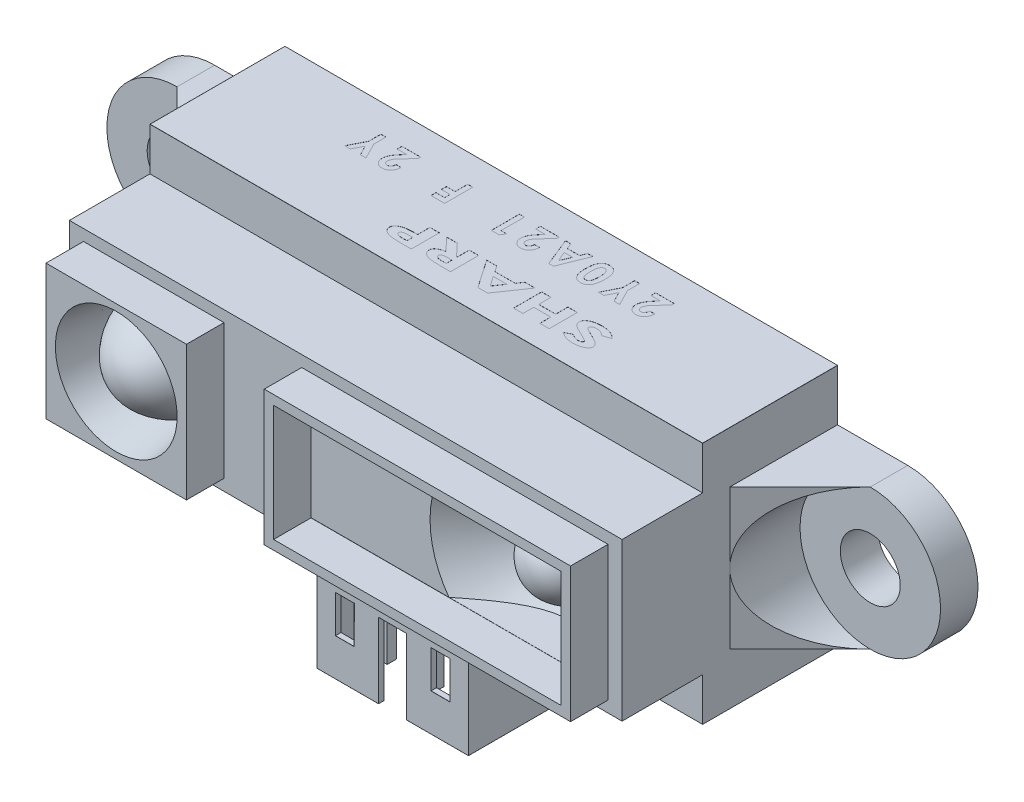
SolidWorks part; units mm, degrees
ref_plane "Front Plane" through (0, 0, 0) normal (0, 0, 1) x (1, 0, 0)
ref_plane "Top Plane" through (0, 0, 0) normal (0, 1, 0) x (1, 0, 0)
ref_plane "Right Plane" through (0, 0, 0) normal (1, 0, 0) x (0, 0, -1)
sketch "Sketch1" plane through (0, 0, 0) normal (0, 0, 1) x (1, 0, 0)
  line L0 (-18.5, 3.75) -> (-14.75, 3.75)
  line L1 (-14.75, -6.5) -> (14.75, -6.5)
  line L2 (-14.75, -6.5) -> (-14.75, -3.75)
  line L3 (-14.75, 6.5) -> (14.75, 6.5)
  line L4 (14.75, -6.5) -> (14.75, -3.75)
  line L5 (0, 0) -> (14.75, 6.5) construction
  line L6 (-14.75, 6.5) -> (0, 0) construction
  line L7 (-18.5, -3.75) -> (-14.75, -3.75)
  line L8 (18.5, -3.75) -> (14.75, -3.75)
  line L9 (18.5, 3.75) -> (14.75, 3.75)
  line L10 (-14.75, 3.75) -> (-14.75, 6.5)
  line L11 (14.75, 3.75) -> (14.75, 6.5)
  line L12 (0, 25.5423) -> (0, -14.0261) construction
  arc A0 (-18.5, 3.75) -> (-18.5, -3.75) centre (-18.5, 0) ccw
  arc A1 (18.5, -3.75) -> (18.5, 3.75) centre (18.5, 0) ccw
  circle A2 centre (-18.5, 0) radius 1.6
  circle A3 centre (18.5, 0) radius 1.6
  point P4 (0, 0)
  dimension "D2" = 37
  dimension "D3" = 18.5
  dimension "D4" = 7.5
  dimension "D5" = 7.5
  dimension "D7" = 3.2
  dimension "D8" = 3.2
  dimension "D1" = 29.5
  dimension "D6" = 13
extrude "Boss-Extrude1" add sketch "Sketch1" along normal blind 13.5
sketch "Sketch3" plane through (0, 0, 0) normal (0, 0, -1) x (-1, 0, 0)
  circle A0 centre (-18.5, 0) radius 3.75
  circle A1 centre (18.5, 0) radius 3.75
extrude "Cut-Extrude1" cut sketch "Sketch3" against normal through all from offset 2 offset against normal yes
sketch "Sketch4" plane through (0, -3.75, 0) normal (0, -1, 0) x (1, 0, 0)
  line L0 (22.25, 2) -> (18.5, 2)
  line L1 (18.5, 2) -> (14.75, 5.75)
  line L2 (14.75, 13.5) -> (14.75, 0) construction
  line L3 (14.75, 5.75) -> (14.75, 13.5)
  line L4 (14.75, 13.5) -> (22.25, 13.5)
  line L5 (22.25, 13.5) -> (22.25, 2)
  line L6 (-22.25, 2) -> (-18.5, 2)
  line L7 (-18.5, 2) -> (-14.75, 5.75)
  line L8 (-14.75, 13.5) -> (-14.75, 0) construction
  line L9 (-14.75, 5.75) -> (-14.75, 13.5)
  line L10 (-14.75, 13.5) -> (-22.25, 13.5)
  line L11 (-22.25, 13.5) -> (-22.25, 2)
  line L12 (14.75, 13.5) -> (14.75, 0) construction
  dimension "D1" = 45
  dimension "D2" = 45
extrude "Cut-Extrude2" cut sketch "Sketch4" against normal through all
sketch "Sketch5" plane through (0, 0, 13.5) normal (0, 0, 1) x (1, 0, 0)
  line L0 (14.75, -6.5) -> (14.75, 6.5) construction
  line L1 (-14.75, 6.5) -> (14.75, 6.5)
  line L2 (-14.75, 6.5) -> (-14.75, 4.2)
  line L3 (-14.75, 4.2) -> (14.75, 4.2)
  line L4 (14.75, 6.5) -> (14.75, 4.2)
  line L6 (-14.75, -6.5) -> (14.75, -6.5)
  line L7 (-14.75, -6.5) -> (-14.75, -4.2)
  line L8 (-14.75, -4.2) -> (14.75, -4.2)
  line L9 (14.75, -6.5) -> (14.75, -4.2)
  dimension "D1" = 8.4
  dimension "D2" = 4.2
extrude "Cut-Extrude3" cut sketch "Sketch5" along normal through all from offset 6.3 offset against normal yes
sketch "Sketch6" plane through (0, 0, 13.5) normal (0, 0, 1) x (1, 0, 0)
  line L0 (-14.75, 4.2) -> (-14.75, -4.2) construction
  line L1 (-14, -3.6) -> (-6.5, -3.6)
  line L2 (-14, -3.6) -> (-14, 3.6)
  line L3 (-14, 3.6) -> (-6.5, 3.6)
  line L4 (14, -3.6) -> (14, 3.6)
  line L5 (-14, -3.6) -> (14, 3.6) construction
  line L6 (-14, 3.6) -> (14, -3.6) construction
  line L7 (-6.5, 3.6) -> (-6.5, -3.6)
  line L8 (-2.35, 3.6) -> (-2.35, -3.6)
  line L9 (-2.35, 3.6) -> (14, 3.6)
  line L10 (-2.35, -3.6) -> (14, -3.6)
  line L12 (-14.75, -4.2) -> (14.75, -4.2)
  line L13 (-14.75, -4.2) -> (-14.75, 4.2)
  line L14 (-14.75, 4.2) -> (14.75, 4.2)
  line L15 (14.75, -4.2) -> (14.75, 4.2)
  line L16 (-14.75, -4.2) -> (14.75, 4.2) construction
  line L17 (-14.75, 4.2) -> (14.75, -4.2) construction
  point P0 (0, 0)
  point P12 (0, 0)
  dimension "D1" = 7.2
  dimension "D2" = 0.75
  dimension "D3" = 7.5
  dimension "D4" = 4.15
  dimension "D5" = 16.35
extrude "Cut-Extrude4" cut sketch "Sketch6" along normal through all from offset 2 offset against normal yes
sketch "Sketch7" plane through (0, 0, 13.5) normal (0, 0, 1) x (1, 0, 0)
  line L0 (-6.5, -3.6) -> (-6.5, 3.6) construction
  line L1 (-6.5, 3.6) -> (-14, 3.6) construction
  circle A0 centre (-10.25, 0) radius 3.25
  point P4 (-6.5, 0)
  point P8 (-10.25, 3.6)
  dimension "D1" = 6.5
extrude "Cut-Extrude5" cut sketch "Sketch7" against normal blind 3 draft 10
sketch "Sketch8" plane through (0, 0, 0) normal (0, 1, 0) x (1, 0, 0)
  line L0 (-10.25, -10.5) -> (-10.25, -17.4091) construction
  line L1 (-12.971, -10.5) -> (-7.529, -10.5) construction
  line L2 (-10.25, -10.5) -> (-7.529, -10.5)
  line L3 (-14, -13.5) -> (-6.5, -13.5) construction
  line L4 (-13.25, -13.5) -> (-7.25, -13.5) construction
  line L5 (-7.529, -13.5) -> (-7.529, -7.5) construction
  line L6 (-10.25, -10.5) -> (-10.25, -13.5)
  spline S0 degree 3 poles (-7.529, -10.5) (-7.529, -11.5) (-8.5833, -13.5) (-10.25, -13.5) knots 0 0 0 0 1 1 1 1
  dimension "D1" = 5
  dimension "D2" = 3
  dimension "D3" = 90
  dimension "D4" = 90
revolve "Revolve1" add sketch "Sketch8" angle 360 about L0
sketch "Sketch9" plane through (0, 0, 13.5) normal (0, 0, 1) x (1, 0, 0)
  line L0 (14, 3.6) -> (-2.35, 3.6) construction
  line L1 (-1.85, -3.1) -> (13.5, -3.1)
  line L2 (-1.85, -3.1) -> (-1.85, 3.1)
  line L3 (-1.85, 3.1) -> (13.5, 3.1)
  line L4 (13.5, -3.1) -> (13.5, 3.1)
  line L5 (-2.35, 3.6) -> (-2.35, -3.6) construction
  line L6 (14, -3.6) -> (14, 3.6) construction
  line L7 (-2.35, -3.6) -> (14, -3.6) construction
  dimension "D1" = 0.5
  dimension "D2" = 0.5
  dimension "D3" = 0.5
  dimension "D4" = 0.5
extrude "Cut-Extrude6" cut sketch "Sketch9" against normal blind 2
sketch "Sketch10" plane through (0, 0, 11.5) normal (0, 0, 1) x (1, 0, 0)
  line L0 (-14.75, 4.2) -> (-14.75, -4.2) construction
  line L1 (14, -3.6) -> (14, 3.6) construction
  line L7 (13.5, -3.1) -> (13.5, 3.1) construction
  circle A2 centre (9.75, 0) radius 2.25
  point P7 (14, 0)
  point P17 (13.5, 0)
  dimension "D2" = 4.5
  dimension "D1" = 24.5
sketch "Sketch12" plane through (0, 0, 0) normal (0, 0, -1) x (-1, 0, 0)
  line L0 (14.75, -6.5) -> (-14.75, -6.5) construction
  line L1 (5.05, -6.5) -> (-5.05, -6.5)
  line L2 (5.05, -6.5) -> (5.05, -12.4)
  line L3 (5.05, -12.4) -> (-5.05, -12.4)
  line L4 (-5.05, -6.5) -> (-5.05, -12.4)
  point P6 (0, -6.5)
  dimension "D1" = 10.1
  dimension "D2" = 5.9
extrude "Boss-Extrude2" add sketch "Sketch12" against normal blind 1.2 from offset 3.3 offset against normal yes
sketch "Sketch13" plane through (0, -6.5, 0) normal (0, -1, 0) x (1, 0, 0)
  line L0 (-14.75, 7.2) -> (14.75, 7.2) construction
  line L1 (5.05, 4.5) -> (-5.05, 4.5)
  line L2 (5.05, 4.5) -> (5.05, 7.2)
  line L3 (5.05, 7.2) -> (-5.05, 7.2)
  line L4 (-5.05, 4.5) -> (-5.05, 7.2)
extrude "Cut-Extrude8" cut sketch "Sketch13" against normal up to surface (2.3 mm away) up to face at (0, -4.2, 9.35)
sketch "Sketch14" plane through (0, -4.2, 0) normal (0, -1, 0) x (1, 0, 0)
  line L0 (5.05, 4.5) -> (-5.05, 4.5) construction
  line L1 (-4.05, 4.5) -> (4.05, 4.5)
  line L2 (-4.05, 4.5) -> (-4.05, 9)
  line L3 (-4.05, 9) -> (4.05, 9)
  line L4 (4.05, 4.5) -> (4.05, 9)
  line L5 (-5.05, 7.2) -> (-5.05, 4.5) construction
  line L6 (-3.75, 4.8) -> (3.75, 4.8)
  line L7 (-3.75, 4.8) -> (-3.75, 8.7)
  line L8 (-3.75, 8.7) -> (3.75, 8.7)
  line L9 (3.75, 4.8) -> (3.75, 8.7)
  line L10 (-2.79, 7) -> (-2.29, 7)
  line L11 (-2.79, 7) -> (-2.79, 6.5)
  line L12 (-2.79, 6.5) -> (-2.29, 6.5)
  line L13 (-2.29, 7) -> (-2.29, 6.5)
  line L14 (-0.25, 7) -> (0.25, 7)
  line L15 (-0.25, 7) -> (-0.25, 6.5)
  line L16 (-0.25, 6.5) -> (0.25, 6.5)
  line L17 (0.25, 7) -> (0.25, 6.5)
  line L18 (2.29, 7) -> (2.79, 7)
  line L19 (2.29, 7) -> (2.29, 6.5)
  line L20 (2.29, 6.5) -> (2.79, 6.5)
  line L21 (2.79, 7) -> (2.79, 6.5)
  point P22 (0, 4.5)
  point P24 (0, 4.8)
  point P25 (0, 6.5)
  point P28 (-2.29, 6.75)
  point P29 (-0.25, 6.75)
  point P30 (2.29, 6.75)
  point P31 (-3.75, 6.75)
  line M23 (-5.05, 4.5) -> (5.05, 4.5)
  dimension "D1" = 4.5
  dimension "D2" = 1
  dimension "D3" = 0.3
  dimension "D4" = 0.3
  dimension "D5" = 0.3
  dimension "D6" = 0.5
  dimension "D7" = 0.5
  dimension "D8" = 0.5
  dimension "D9" = 0.5
  dimension "D10" = 0.5
  dimension "D11" = 0.5
  dimension "D12" = 2.54
  dimension "D13" = 2.54
extrude "Boss-Extrude3" add sketch "Sketch14" along normal through all contours L4 L3 L2 L9 L6 L7 L8 M23 | L17 L14 L15 L16 | L21 L20 L19 L18 | L12 L13 L10 L11
sketch "Sketch15" plane through (0, -4.2, 0) normal (0, -1, 0) x (1, 0, 0)
  line L1 (-3.75, 4.8) -> (3.75, 4.8)
  line L2 (-3.75, 4.8) -> (-3.75, 8.7)
  line L3 (-3.75, 8.7) -> (3.75, 8.7)
  line L4 (3.75, 4.8) -> (3.75, 8.7)
extrude "Boss-Extrude4" add sketch "Sketch15" along normal blind 1 from offset 1.5
sketch "Sketch16" plane through (0, 0, 9) normal (0, 0, 1) x (1, 0, 0)
  line L0 (-4.05, -4.2) -> (-4.05, -4.8602)
  line L1 (-4.05, -12.4) -> (-4.05, -4.2) construction
  line L2 (-4.05, -4.8602) -> (-3.55, -4.8602)
  line L3 (-3.55, -4.8602) -> (-3.55, -5.7602)
  line L4 (-3.55, -5.7602) -> (3.55, -5.7602)
  line L5 (3.55, -5.7602) -> (3.55, -4.8)
  line L6 (3.55, -4.8) -> (4.05, -4.8)
  line L7 (4.05, -12.4) -> (4.05, -4.2) construction
  line L8 (4.05, -4.8) -> (4.05, -4.2)
  line L9 (-4.05, -12.4) -> (-4.05, -4.2) construction
  line L10 (-4.05, -4.2) -> (4.05, -4.2)
  dimension "D1" = 0.6
  dimension "D2" = 0.9
  dimension "D3" = 0.5
  dimension "D4" = 0.5
extrude "Cut-Extrude9" cut sketch "Sketch16" against normal up to surface (4.5 mm away) up to face at (-4.65, -7.94, 4.5)
sketch "Sketch17" plane through (0, -12.4, 0) normal (0, -1, 0) x (-1, 0, 0)
  line L0 (4.05, -4.5) -> (4.05, -9) construction
  line L1 (-4.05, -4.5) -> (4.05, -4.5)
  line L2 (-4.05, -4.5) -> (-4.05, -4.6)
  line L3 (-4.05, -4.6) -> (4.05, -4.6)
  line L4 (4.05, -4.5) -> (4.05, -4.6)
  point P7 (4.05, -4.55)
  dimension "D1" = 0.05
extrude "Cut-Extrude10" cut sketch "Sketch17" against normal blind 0.1
chamfer "Chamfer3" distance 0.05 12 edges at (2.29, -12.4, 6.75) (2.54, -12.4, 7) (2.79, -12.4, 6.75) (2.54, -12.4, 6.5) (-0.25, -12.4, 6.75) (0, -12.4, 7) (0.25, -12.4, 6.75) (0, -12.4, 6.5) (-2.79, -12.4, 6.75) (-2.54, -12.4, 7) (-2.29, -12.4, 6.75) (-2.54, -12.4, 6.5)
sketch "Sketch18" plane through (0, 0, 9) normal (0, 0, 1) x (1, 0, 0)
  line L0 (-4.05, -12.4) -> (4.05, -12.4) construction
  line L1 (-0.75, -12.4) -> (0.75, -12.4)
  line L2 (-0.75, -12.4) -> (-0.75, -8.4)
  line L3 (-0.75, -8.4) -> (0.75, -8.4)
  line L4 (0.75, -12.4) -> (0.75, -8.4)
  line L5 (-4.05, -12.3) -> (-4.05, -4.8602) construction
  line L6 (-3.05, -8.4) -> (-2.05, -8.4)
  line L7 (-3.05, -8.4) -> (-3.05, -10.4)
  line L8 (-3.05, -10.4) -> (-2.05, -10.4)
  line L9 (-2.05, -8.4) -> (-2.05, -10.4)
  line L10 (2.05, -8.4) -> (3.05, -8.4)
  line L11 (2.05, -8.4) -> (2.05, -10.4)
  line L12 (2.05, -10.4) -> (3.05, -10.4)
  line L13 (3.05, -8.4) -> (3.05, -10.4)
  line L14 (4.05, -12.4) -> (4.05, -4.8) construction
  point P14 (0, -12.4)
  dimension "D1" = 2
  dimension "D2" = 1
  dimension "D3" = 1
  dimension "D4" = 2
  dimension "D5" = 2
  dimension "D6" = 1
  dimension "D7" = 2
  dimension "D8" = 1
  dimension "D9" = 1.5
  dimension "D10" = 4
extrude "Cut-Extrude11" cut sketch "Sketch18" against normal up to surface (0.3 mm away) up to face at (0, -9.55, 8.7)
fillet "Fillet1" radius 0.005 55 edges at (14.75, 6.5, 3.6) (-14.75, 6.5, 3.6) (0, 6.5, 7.2) (13.5, 0, 11.5) (5.825, -3.1, 11.5) (-2.4, -12.4, 9) (4.05, -8.6, 9) (3.75, -12.4, 6.75) (3.75, -9.55, 8.7) (0, -12.4, 4.8) (-3.75, -9.55, 8.7) (-4.05, -8.6301, 9) (-3.75, -12.4, 6.75) (-2.25, -12.4, 8.7) (0, -6.7, 8.7) (-4.05, -4.8602, 6.75) (-3.8, -4.8602, 9) (-3.55, -5.3102, 9) (0, -5.7602, 9) (3.55, -5.2801, 9) (3.8, -4.8, 9) (-3.8, -4.8602, 4.5) (-4.05, -8.5801, 4.5) (-4.05, -12.4, 6.8) (4.05, -12.4, 6.8) (0, -12.3, 4.5) (-4.05, -12.3, 4.55) (-4.05, -12.35, 4.6) (0, -12.4, 4.6) (2.4, -12.4, 9) (2.25, -12.4, 8.7) (2.05, -9.4, 9) (2.55, -10.4, 9) (3.05, -9.4, 9) (2.55, -8.4, 9) (2.05, -9.4, 8.7) (2.55, -8.4, 8.7) (3.05, -9.4, 8.7) (2.55, -10.4, 8.7) (-3.05, -9.4, 9) (-2.55, -10.4, 9) (-2.05, -9.4, 9) (-2.55, -8.4, 9) (-3.05, -9.4, 8.7) (-2.55, -8.4, 8.7) (-2.05, -9.4, 8.7) (-2.55, -10.4, 8.7) (-0.75, -12.4, 8.85) (0.75, -12.4, 8.85) (-0.75, -10.4, 9) (0.75, -10.4, 9) (0, -8.4, 9) (-0.75, -10.4, 8.7) (0, -8.4, 8.7) (0.75, -10.4, 8.7)
sketch "Sketch19" plane through (0, 6.5, 0) normal (0, 1, 0) x (1, 0, 0)
  line L0 (-8.6216, -1.5) -> (7.745, -1.5) construction
  line L1 (-3.8692, -4.5) -> (7.745, -4.5) construction
  line L2 (14.745, -7.195) -> (14.745, 0) construction
  line L3 (14.745, 0) -> (-14.745, 0) construction
  text T0 "<b>SHARP</b>" font "Century Gothic" height 1.5
  text T1 "<b>2Y0A21  F  2Y</b>" font "Century Gothic" height 1.5
  point P11 (-0.4383, -1.5)
  dimension "D1" = 7
  dimension "D2" = 7
  dimension "D3" = 1.5
  dimension "D4" = 3
extrude "Cut-Extrude12" cut sketch "Sketch19" against normal blind 0.005
extrude "Cut-Extrude13" cut sketch "Sketch10" against normal blind 3
sketch "Sketch21" plane through (0, 0, 0) normal (0, 1, 0) x (1, 0, 0)
  line L0 (9.75, -8.5) -> (9.75, -21.6727) construction
  line L1 (7.5, -8.5) -> (12, -8.5) construction
  line L2 (-2.35, -11.5) -> (14, -11.5) construction
  line L3 (4.5, -11.5) -> (9.75, -11.5)
  line L4 (9.75, -8.5) -> (7.5, -8.5)
  line L5 (7.5, -8.5) -> (4.5, -11.5)
  line L6 (9.75, -8.5) -> (9.75, -11.5)
  dimension "D1" = 2.25
  dimension "D2" = 45
sketch "Sketch22" plane through (0, 0, 8.5) normal (0, 0, 1) x (1, 0, 0)
  circle A0 centre (9.75, 0) radius 2.25
sweep "Cut-Sweep1" cut profiles "Sketch21" path "Sketch22"
sketch "Sketch24" plane through (0, 0, 11.5) normal (0, 0, 1) x (1, 0, 0)
  line L0 (4.0461, 3.1) -> (4.0461, 4.2)
  line L1 (5.513, 3.1) -> (-1.85, 3.1) construction
  line L2 (6.6, 4.2) -> (-14.75, 4.2) construction
  line L3 (4.0461, 4.2) -> (14.75, 4.2)
  line L4 (14.75, 4.2) -> (14.75, -4.2)
  line L5 (14.75, -4.2) -> (4.0461, -4.2)
  line L6 (-14.75, -4.2) -> (6.6, -4.2) construction
  line L7 (4.0461, -4.2) -> (4.0461, -3.095)
  line L8 (-1.85, -3.095) -> (5.5093, -3.095) construction
  line L9 (4.0461, -3.095) -> (13.5, -3.095)
  line L10 (13.5, -3.095) -> (13.5, 3.1)
  line L11 (13.5, 3.1) -> (4.0461, 3.1)
  line L13 (13.5, 3.1) -> (13.5, -3.1) construction
extrude "Boss-Extrude5" add sketch "Sketch24" against normal up to surface (4.3 mm away) up to face at (0, 5.3475, 7.2)
sketch "Sketch25" plane through (0, 0, 0) normal (0, 1, 0) x (1, 0, 0)
  line L0 (9.75, -8.5) -> (9.75, -25.3837) construction
  line L1 (7.5, -8.5) -> (12, -8.5) construction
  line L2 (9.75, -8.5) -> (12, -8.5)
  line L3 (14, -11.5) -> (-2.35, -11.5) construction
  line L4 (12, -11.5) -> (12, -5.5) construction
  line L5 (3.75, -11.5) -> (15.75, -11.5) construction
  line L6 (9.75, -8.5) -> (9.75, -11.5)
  spline S0 degree 3 poles (12, -8.5) (12, -9.5) (11.4167, -11.5) (9.75, -11.5) knots 0 0 0 0 1 1 1 1
  dimension "D1" = 3
  dimension "D2" = 5
  dimension "D3" = 90
  dimension "D4" = 90
revolve "Revolve4" add sketch "Sketch25" angle 360 about L0
